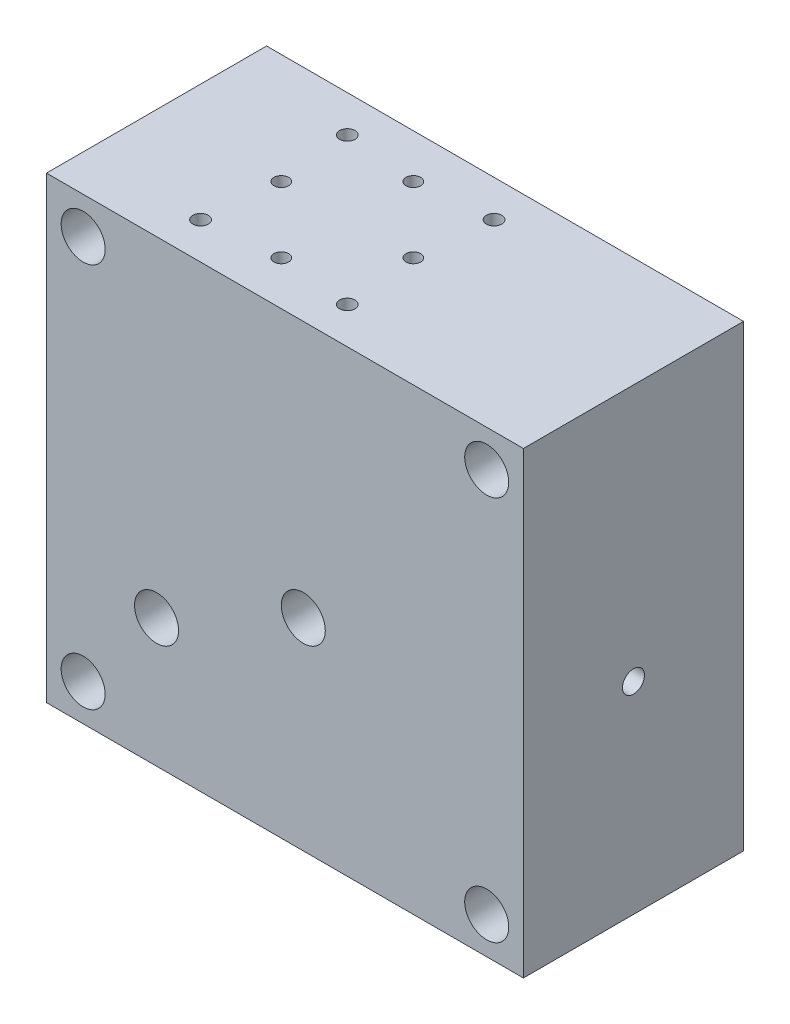
SolidWorks part; units mm, degrees
ref_plane "前视基准面" through (0, 0, 0) normal (0, 0, 1) x (1, 0, 0)
ref_plane "上视基准面" through (0, 0, 0) normal (0, 1, 0) x (1, 0, 0)
ref_plane "右视基准面" through (0, 0, 0) normal (1, 0, 0) x (0, 0, -1)
sketch "草图1" plane through (0, 0, 0) normal (0, 0, 1) x (1, 0, 0)
  line L1 (-65, -62.5) -> (65, -62.5)
  line L2 (-65, -62.5) -> (-65, 62.5)
  line L3 (-65, 62.5) -> (65, 62.5)
  line L4 (65, -62.5) -> (65, 62.5)
  line L5 (-65, -62.5) -> (65, 62.5) construction
  line L6 (-65, 62.5) -> (65, -62.5) construction
  circle A0 centre (-55, -52.5) radius 6
  circle A1 centre (55, -52.5) radius 6
  circle A2 centre (55, 52.5) radius 6
  circle A3 centre (-55, 52.5) radius 6
  point P0 (0, 0)
  dimension "D1" = 10
  dimension "D2" = 10
  dimension "D5" = 130
  dimension "D6" = 125
  dimension "D3" = 2
  dimension "D4" = 2
ref_plane "基准面1" through (0, 62.5, 0) normal (0, 1, 0) x (1, 0, 0)
sketch "草图3" plane through (0, 62.5, 0) normal (0, 1, 0) x (1, 0, 0)
  line L2 (-13, 60) -> (-13, 0) construction
  line L4 (-65, 30) -> (65, 30) construction
  circle A0 centre (-13, 30) radius 18 construction
  circle A1 centre (-13, 12) radius 2
  point P0 (-33, 10)
  point P8 (7, 10)
  point P9 (7, 50)
  point P10 (-33, 50)
  point P19 (-13, 48)
  point P20 (5, 30)
  point P21 (-13, 12)
  point P22 (-31, 30)
  dimension "D3" = 2
  dimension "D4" = 2
extrude "凸台-拉伸1" add sketch "草图1" against normal blind 60 contours A1 | A2 | A0 | L2 L3 L4 L1 | A3
sketch "草图4" plane through (0, 0, 0) normal (0, 0, 1) x (1, 0, 0)
  line L0 (-65, 62.5) -> (-65, -7.5)
  line L1 (-65, 62.5) -> (65, 62.5) construction
  line L2 (-65, -62.5) -> (-65, 62.5) construction
  line L3 (-65, -7.5) -> (5, -7.5)
hole_wizard "Ø12.0 (12) 直径孔1" positions "3D草图1" profile "草图5" hole size "Ø12.0" standard "GB"
sketch3d "3D草图1"
  point P0 (5, -7.5, 0)
sketch "草图5" plane through (5, -7.5, 0) normal (1, 0, 0) x (0, -1, 0)
  line L0 (0, 0) -> (0, 33.6052)
  line L1 (0, 33.6052) -> (6, 30)
  line L2 (6, 30) -> (6, 0)
  line L5 (6, 0) -> (0, 0)
  line L10 (0, 33.6052) -> (-6, 30) construction
  line L11 (0, -6.35) -> (0, 107.95) construction
  dimension "孔直径" = 12
  dimension "孔深度" = 30
  dimension "导头角度" = 118
sketch "草图6" plane through (0, 0, 0) normal (0, 0, 1) x (1, 0, 0)
  line L0 (-65, 62.5) -> (-65, -27.5)
  line L1 (-65, -62.5) -> (-65, 62.5) construction
  line L2 (-65, -27.5) -> (-35, -27.5)
hole_wizard "Ø12.0 (12) 直径孔2" positions "3D草图2" profile "草图7" hole size "Ø12.0" standard "GB"
sketch3d "3D草图2"
  point P0 (-35, -27.5, 0)
sketch "草图7" plane through (-35, -27.5, 0) normal (1, 0, 0) x (0, -1, 0)
  line L0 (0, 0) -> (0, 15.6052)
  line L1 (0, 15.6052) -> (6, 12)
  line L2 (6, 12) -> (6, 0)
  line L5 (6, 0) -> (0, 0)
  line L10 (0, 15.6052) -> (-6, 12) construction
  line L11 (0, -6.35) -> (0, 107.95) construction
  dimension "孔直径" = 12
  dimension "孔深度" = 12
  dimension "导头角度" = 118
hole_wizard "Ø4.0 (4) 直径孔1" positions "草图10" profile "草图11" hole size "Ø4.0" standard "GB" end condition through all
sketch "草图10" plane through (0, 62.5, 0) normal (0, 1, 0) x (1, 0, 0)
  point P0 (-13, 48)
  point P3 (-31, 30)
sketch "草图11" plane through (-13, 62.5, -48) normal (1, 0, 0) x (0, 0, 1)
  line L0 (0, 0) -> (0, 125)
  line L1 (0, 125) -> (2, 125)
  line L2 (2, 125) -> (2, 0)
  line L5 (2, 0) -> (0, 0)
  line L11 (0, -6.35) -> (0, 107.95) construction
  dimension "通孔孔直径" = 4
  dimension "通孔孔深度" = 125
hole_wizard "M10 螺纹孔2" positions "草图12" profile "草图13" tap size "M10" standard "GB"
sketch "草图12" plane through (0, -62.5, 0) normal (0, -1, 0) x (-1, 0, 0)
  point P0 (31, 30)
  point P3 (13, 48)
sketch "草图13" plane through (-31, -62.5, -30) normal (1, 0, 0) x (0, 0, -1)
  line L0 (0, 0) -> (0, 16.5537)
  line L1 (0, 16.5537) -> (4.25, 14)
  line L2 (4.25, 14) -> (4.25, 0)
  line L5 (4.25, 0) -> (0, 0)
  line L10 (0, 16.5537) -> (-4.25, 14) construction
  line L11 (0, -6.35) -> (0, 107.95) construction
  dimension "螺纹孔钻头直径" = 8.5
  dimension "螺纹孔钻头深度" = 14
  dimension "导头角度" = 118
cosmetic thread "孔螺蚊线1" parameters "D1"=12, "D2"=10
cosmetic thread "孔螺蚊线2" parameters "D1"=12, "D2"=10
hole_wizard "M5 螺纹孔2" positions "草图16" profile "草图15" tap size "M5" standard "GB"
sketch "草图16" plane through (0, 62.5, 0) normal (0, 1, 0) x (1, 0, 0)
  point P0 (-33, 50)
  point P3 (7, 50)
  point P6 (7, 10)
  point P9 (-33, 10)
sketch "草图15" plane through (-33, 62.5, -50) normal (1, 0, 0) x (0, 0, 1)
  line L0 (0, 0) -> (0, 15.2618)
  line L1 (0, 15.2618) -> (2.1, 14)
  line L2 (2.1, 14) -> (2.1, 0)
  line L5 (2.1, 0) -> (0, 0)
  line L10 (0, 15.2618) -> (-2.1, 14) construction
  line L11 (0, -6.35) -> (0, 107.95) construction
  dimension "螺纹孔钻头直径" = 4.2
  dimension "螺纹孔钻头深度" = 14
  dimension "导头角度" = 118
cosmetic thread "孔螺蚊线3" parameters "D1"=10, "D2"=5
cosmetic thread "孔螺蚊线4" parameters "D1"=10, "D2"=5
cosmetic thread "孔螺蚊线5" parameters "D1"=10, "D2"=5
cosmetic thread "孔螺蚊线6" parameters "D1"=10, "D2"=5
sketch "草图17" plane through (-65, 0, 0) normal (-1, 0, 0) x (0, 0, 1)
  line L0 (0, 62.5) -> (-12, 62.5)
  line L1 (-12, 62.5) -> (-12, 23.5)
hole_wizard "Ø8.0 (8) 直径孔2" positions "3D草图6" profile "草图18" hole size "Ø8.0" standard "GB"
sketch3d "3D草图6"
  point P0 (-65, 23.5, -12)
sketch "草图18" plane through (-65, 23.5, -12) normal (0, 1, 0) x (0, 0, 1)
  line L0 (0, 0) -> (0, 54.4034)
  line L1 (0, 54.4034) -> (4, 52)
  line L2 (4, 52) -> (4, 0)
  line L5 (4, 0) -> (0, 0)
  line L10 (0, 54.4034) -> (-4, 52) construction
  line L11 (0, -6.35) -> (0, 107.95) construction
  dimension "孔直径" = 8
  dimension "孔深度" = 52
  dimension "导头角度" = 118
hole_wizard "M10 螺纹孔3" positions "3D草图7" profile "草图19" tap size "M10" standard "GB"
sketch3d "3D草图7"
  point P0 (-65, 23.5, -12)
sketch "草图19" plane through (-65, 23.5, -12) normal (0, 1, 0) x (0, 0, 1)
  line L0 (0, 0) -> (0, 10.5537)
  line L1 (0, 10.5537) -> (4.25, 8)
  line L2 (4.25, 8) -> (4.25, 0)
  line L5 (4.25, 0) -> (0, 0)
  line L10 (0, 10.5537) -> (-4.25, 8) construction
  line L11 (0, -6.35) -> (0, 107.95) construction
  dimension "螺纹孔钻头直径" = 8.5
  dimension "螺纹孔钻头深度" = 8
  dimension "导头角度" = 118
cosmetic thread "孔螺蚊线7" parameters "D1"=6, "D2"=10
sketch "草图20" plane through (0, -62.5, 0) normal (0, -1, 0) x (-1, 0, 0)
  line L0 (65, 0) -> (65, 12)
  line L1 (65, 60) -> (65, 0) construction
  line L2 (65, 12) -> (35, 12)
hole_wizard "Ø8.0 (8) 直径孔3" positions "3D草图8" profile "草图21" hole size "Ø8.0" standard "GB"
sketch3d "3D草图8"
  point P0 (-35, -62.5, -12)
sketch "草图21" plane through (-35, -62.5, -12) normal (1, 0, 0) x (0, 0, -1)
  line L0 (0, 0) -> (0, 88.4034)
  line L1 (0, 88.4034) -> (4, 86)
  line L2 (4, 86) -> (4, 0)
  line L5 (4, 0) -> (0, 0)
  line L10 (0, 88.4034) -> (-4, 86) construction
  line L11 (0, -6.35) -> (0, 107.95) construction
  dimension "孔直径" = 8
  dimension "孔深度" = 86
  dimension "导头角度" = 118
sketch "草图24" plane through (0, 62.5, 0) normal (0, 1, 0) x (1, 0, 0)
  line L0 (-13, 12) -> (-13, 0)
extrude "切除-拉伸1" cut sketch "草图3" against normal blind 39 contours A1
sketch "草图30" plane through (0, 0, 0) normal (0, 0, 1) x (1, 0, 0)
  line L0 (0, 0) -> (65, 0)
  line L1 (65, -62.5) -> (65, 62.5) construction
  line L2 (65, 0) -> (65, -62.5)
  point P0 (65, -59.4908)
ref_plane "基准面2" through (65, 0, 0) normal (1, 0, 0) x (0, 0, -1)
sketch "草图31" plane through (65, 0, 0) normal (1, 0, 0) x (0, 0, -1)
  line L0 (0, -62.5) -> (30, -62.5)
  line L1 (30, -62.5) -> (30, -7.5)
  circle A0 centre (30, -7.5) radius 3
extrude "切除-拉伸2" cut sketch "草图31" against normal blind 60 contours A0
sketch "草图32" plane through (0, 62.5, 0) normal (0, 1, 0) x (1, 0, 0)
  circle A0 centre (5, 30) radius 2
extrude "切除-拉伸3" cut sketch "草图32" against normal blind 69
hole_wizard "M10 螺纹孔4" positions "3D草图10" profile "草图34" tap size "M10" standard "GB"
sketch3d "3D草图10"
  point P0 (-35, -62.5, -12)
sketch "草图34" plane through (-35, -62.5, -12) normal (1, 0, 0) x (0, 0, -1)
  line L0 (0, 0) -> (0, 16.0537)
  line L1 (0, 16.0537) -> (4.25, 13.5)
  line L2 (4.25, 13.5) -> (4.25, 0)
  line L5 (4.25, 0) -> (0, 0)
  line L10 (0, 16.0537) -> (-4.25, 13.5) construction
  line L11 (0, -6.35) -> (0, 107.95) construction
  dimension "螺纹孔钻头直径" = 8.5
  dimension "螺纹孔钻头深度" = 13.5
  dimension "导头角度" = 118
cosmetic thread "孔螺蚊线8" parameters "D1"=6, "D2"=10
